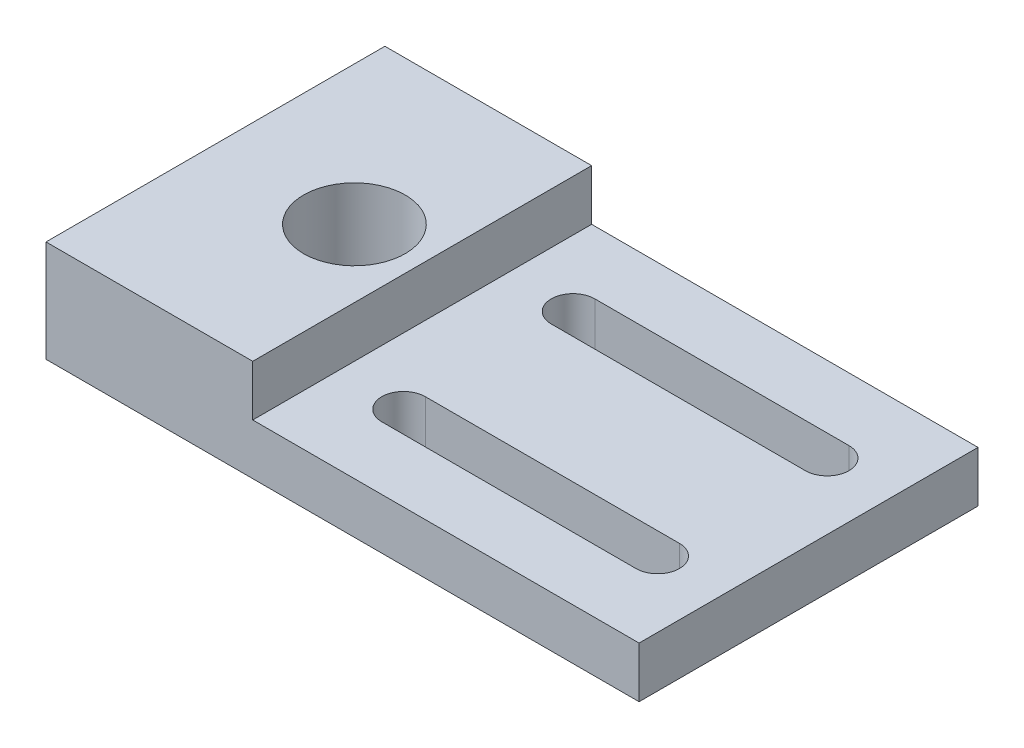
SolidWorks part; units mm, degrees
material "ABS"
ref_plane "Front Plane" through (0, 0, 0) normal (0, 0, 1) x (1, 0, 0)
ref_plane "Top Plane" through (0, 0, 0) normal (0, 1, 0) x (1, 0, 0)
ref_plane "Right Plane" through (0, 0, 0) normal (1, 0, 0) x (0, 0, -1)
sketch "Sketch1" plane through (0, 0, 0) normal (0, 0, 1) x (1, 0, 0)
  line L0 (-22.225, 7.62) -> (-6.731, 7.62)
  line L1 (-6.731, 7.62) -> (-6.731, 3.81)
  line L2 (-6.731, 3.81) -> (22.225, 3.81)
  line L3 (22.225, 3.81) -> (22.225, 0)
  line L4 (22.225, 0) -> (-22.225, 0)
  line L5 (-22.225, 0) -> (-22.225, 7.62)
  dimension "D1" = 44.45
  dimension "D2" = 7.62
  dimension "D3" = 3.81
  dimension "D4" = 15.494
extrude "Boss-Extrude1" add sketch "Sketch1" along normal mid plane 25.4
sketch "Sketch2" plane through (0, 7.62, 0) normal (0, 1, 0) x (1, 0, 0)
  line L0 (-1.778, 6.35) -> (17.272, 6.35) construction
  line L1 (-1.778, 7.9819) -> (17.272, 7.9819)
  line L2 (-1.778, 4.718) -> (17.272, 4.718)
  line L3 (-1.778, -6.35) -> (17.272, -6.35) construction
  line L4 (-1.778, -4.718) -> (17.272, -4.718)
  line L5 (-1.778, -7.9819) -> (17.272, -7.9819)
  line L6 (-6.731, 0) -> (22.225, 0) construction
  line L7 (-6.731, -12.7) -> (-6.731, 12.7) construction
  line L8 (22.225, -12.7) -> (22.225, 12.7) construction
  line L9 (7.747, 12.7) -> (7.747, -12.7) construction
  line L10 (22.225, 12.7) -> (-6.731, 12.7) construction
  line L11 (22.225, -12.7) -> (-6.731, -12.7) construction
  line L12 (15.5482, 12.7) -> (15.5482, 0) construction
  circle A0 centre (-11.811, 0) radius 3.81
  arc A1 (-1.778, 7.9819) -> (-1.778, 4.718) centre (-1.778, 6.35) ccw
  arc A2 (17.272, 4.718) -> (17.272, 7.9819) centre (17.272, 6.35) ccw
  arc A3 (-1.778, -4.718) -> (-1.778, -7.9819) centre (-1.778, -6.35) ccw
  arc A4 (17.272, -7.9819) -> (17.272, -4.718) centre (17.272, -6.35) ccw
  circle A5 centre (-11.811, 0) radius 5.3886 construction
  point P4 (7.747, 6.35)
  point P9 (7.747, -6.35)
  point P31 (15.5482, 6.35)
  dimension "D1" = 7.62
  dimension "D5" = 10.7772
  dimension "D2" = 3.2639
  dimension "D3" = 19.05
  dimension "D4" = 5.08
extrude "Cut-Extrude1" cut sketch "Sketch2" against normal through all
sketch "Sketch3" plane through (0, 0, 0) normal (0, -1, 0) x (1, 0, 0)
  circle A0 centre (-11.811, 0) radius 5.3886
  circle A1 centre (-11.811, 0) radius 5.3886 construction
split line "Split Line1"
